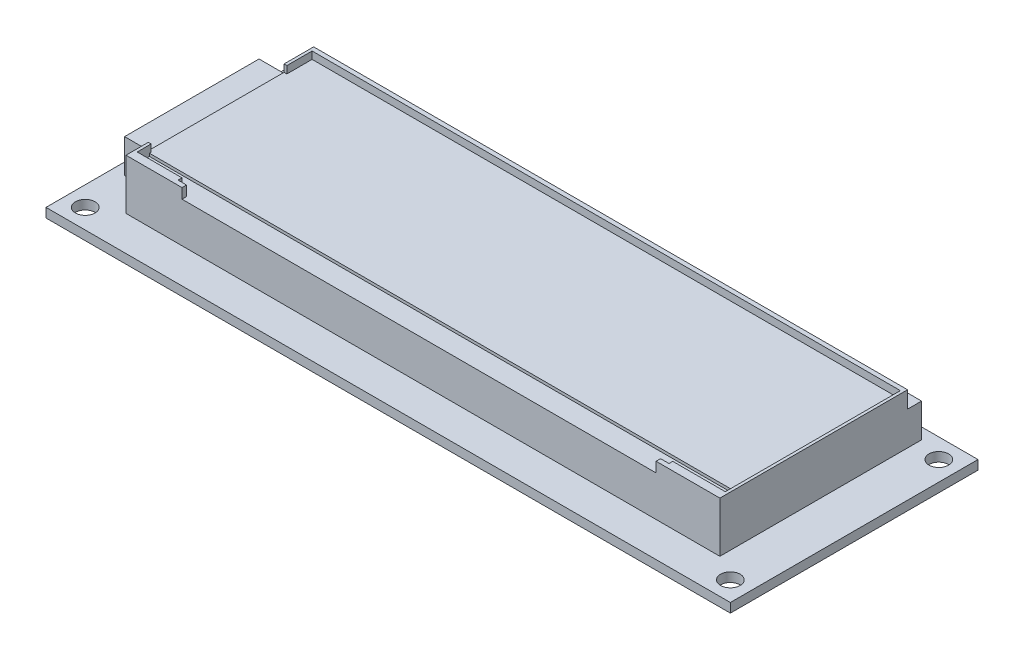
SolidWorks part; units mm, degrees
ref_plane "Front Plane" through (0, 0, 0) normal (0, 0, 1) x (1, 0, 0)
ref_plane "Top Plane" through (0, 0, 0) normal (0, 1, 0) x (1, 0, 0)
ref_plane "Right Plane" through (0, 0, 0) normal (1, 0, 0) x (0, 0, -1)
sketch "Sketch1" plane through (0, 0, 0) normal (0, 1, 0) x (1, 0, 0)
  line L0 (122.15, 22.1) -> (0, 22.1) construction
  line L1 (0, 0) -> (122.15, 0)
  line L2 (0, 0) -> (0, 44.2)
  line L3 (0, 44.2) -> (122.15, 44.2)
  line L4 (122.15, 0) -> (122.15, 44.2)
  line L5 (61.075, 44.2) -> (61.075, 0) construction
  circle A0 centre (3.5, 40.7) radius 1.75
  circle A2 centre (3.5, 3.5) radius 1.75
  circle A3 centre (118.65, 3.5) radius 1.75
  circle A4 centre (118.65, 40.7) radius 1.75
  dimension "D3" = 3.5
  dimension "D4" = 3.5
  dimension "D1" = 122.15
  dimension "D2" = 44.2
  dimension "D5" = 3.5
extrude "Boss-Extrude1" add sketch "Sketch1" along normal blind 1.65
sketch "Sketch2" plane through (0, 1.65, 0) normal (0, 1, 0) x (1, 0, 0)
  line L0 (61.075, 44.2) -> (61.075, 0) construction
  line L1 (8.075, 42.2) -> (114.075, 42.2)
  line L2 (8.075, 42.2) -> (8.075, 6.2)
  line L3 (8.075, 6.2) -> (114.075, 6.2)
  line L4 (114.075, 42.2) -> (114.075, 6.2)
  line L5 (122.15, 44.2) -> (0, 44.2) construction
  line L6 (0, 0) -> (122.15, 0) construction
  point P10 (61.075, 42.2)
  point P11 (0, 0)
  dimension "D1" = 106
  dimension "D2" = 36
  dimension "D3" = 2
extrude "Boss-Extrude2" add sketch "Sketch2" along normal blind 9
sketch "Sketch3" plane through (0, 10.65, 0) normal (0, 1, 0) x (1, 0, 0)
  line L0 (114.075, 42.2) -> (8.075, 42.2) construction
  line L1 (8.075, 42.2) -> (114.075, 42.2)
  line L2 (8.075, 42.2) -> (8.075, 39.7)
  line L3 (8.075, 39.7) -> (114.075, 39.7)
  line L4 (114.075, 42.2) -> (114.075, 39.7)
  line L5 (114.075, 42.2) -> (8.075, 42.2) construction
  line L6 (114.075, 6.2) -> (114.075, 42.2) construction
  line L7 (8.075, 42.2) -> (8.075, 6.2) construction
  dimension "D1" = 2.5
extrude "Cut-Extrude1" cut sketch "Sketch3" against normal blind 3
sketch "Sketch4" plane through (0, 10.65, 0) normal (0, 1, 0) x (1, 0, 0)
  line L0 (16.575, 7.7) -> (16.575, 7)
  line L1 (8.575, 38.92) -> (113.575, 38.92)
  line L4 (113.575, 38.92) -> (113.575, 7.6721)
  line L5 (8.075, 39.7) -> (114.075, 39.7) construction
  line L6 (114.075, 6.2) -> (114.075, 39.7) construction
  line L7 (8.575, 7.7) -> (16.575, 7.7)
  line L8 (8.575, 38.92) -> (8.575, 34.42)
  line L9 (8.575, 34.42) -> (8.075, 34.42)
  line L10 (8.075, 39.7) -> (8.075, 6.2) construction
  line L11 (8.075, 34.42) -> (8.075, 10.2)
  line L12 (8.075, 42.2) -> (8.075, 6.2) construction
  line L13 (8.075, 10.2) -> (8.575, 10.2)
  line L14 (8.575, 10.2) -> (8.575, 7.7)
  line L15 (16.575, 7) -> (18.075, 7)
  line L16 (18.075, 7) -> (18.075, 6.2)
  line L17 (8.075, 6.2) -> (114.075, 6.2) construction
  line L18 (18.075, 6.2) -> (102.6897, 6.2)
  line L19 (102.6897, 6.2) -> (102.6897, 7)
  line L20 (102.6897, 7) -> (104.1897, 7)
  line L21 (104.1897, 7) -> (104.1897, 7.6721)
  line L22 (104.1897, 7.6721) -> (113.575, 7.6721)
  line L23 (8.075, 6.2) -> (114.075, 6.2) construction
  dimension "D1" = 1.5
  dimension "D2" = 0.78
  dimension "D3" = 0.5
  dimension "D4" = 4.5
  dimension "D5" = 2.5
  dimension "D6" = 0.5
  dimension "D7" = 10
  dimension "D8" = 1.5
  dimension "D9" = 0.8
extrude "Cut-Extrude2" cut sketch "Sketch4" against normal blind 1.3
sketch "Sketch5" plane through (0, 1.65, 0) normal (0, 1, 0) x (1, 0, 0)
  line L0 (8.075, 42.2) -> (8.075, 6.2) construction
  line L1 (8.075, 35.95) -> (2.075, 35.95)
  line L2 (8.075, 35.95) -> (8.075, 11.95)
  line L3 (8.075, 11.95) -> (2.075, 11.95)
  line L4 (2.075, 35.95) -> (2.075, 11.95)
  line L5 (8.075, 6.2) -> (18.075, 6.2) construction
  dimension "D1" = 24
  dimension "D2" = 6
  dimension "D3" = 5.75
extrude "Boss-Extrude3" add sketch "Sketch5" along normal blind 6
sketch "Sketch6" plane through (0, 9.35, 0) normal (0, 1, 0) x (1, 0, 0)
  line L0 (113.575, 7.6721) -> (113.575, 38.92) construction
  line L2 (8.575, 7.7) -> (8.575, 9.9)
  line L3 (8.575, 9.9) -> (113.575, 9.9)
  line L4 (113.575, 7.6721) -> (113.575, 9.9)
  line L5 (8.575, 7.7) -> (16.575, 7.7)
  line L6 (16.575, 7.7) -> (16.575, 7)
  line L7 (16.575, 7.7) -> (16.575, 7) construction
  line L8 (16.575, 7) -> (18.075, 7)
  line L9 (16.575, 7) -> (18.075, 7) construction
  line L10 (18.075, 7) -> (18.075, 6.2)
  line L11 (18.075, 6.2) -> (102.6897, 6.2)
  line L12 (102.6897, 6.2) -> (102.6897, 7)
  line L13 (102.6897, 7) -> (104.1897, 7)
  line L14 (104.1897, 7) -> (104.1897, 7.6721)
  line L15 (104.1897, 7.6721) -> (113.575, 7.6721)
  point P20 (0, 0)
  point P25 (0, 0)
  point P27 (0, 0)
  dimension "D1" = 2.2
extrude "Cut-Extrude3" cut sketch "Sketch6" against normal blind 0.5
